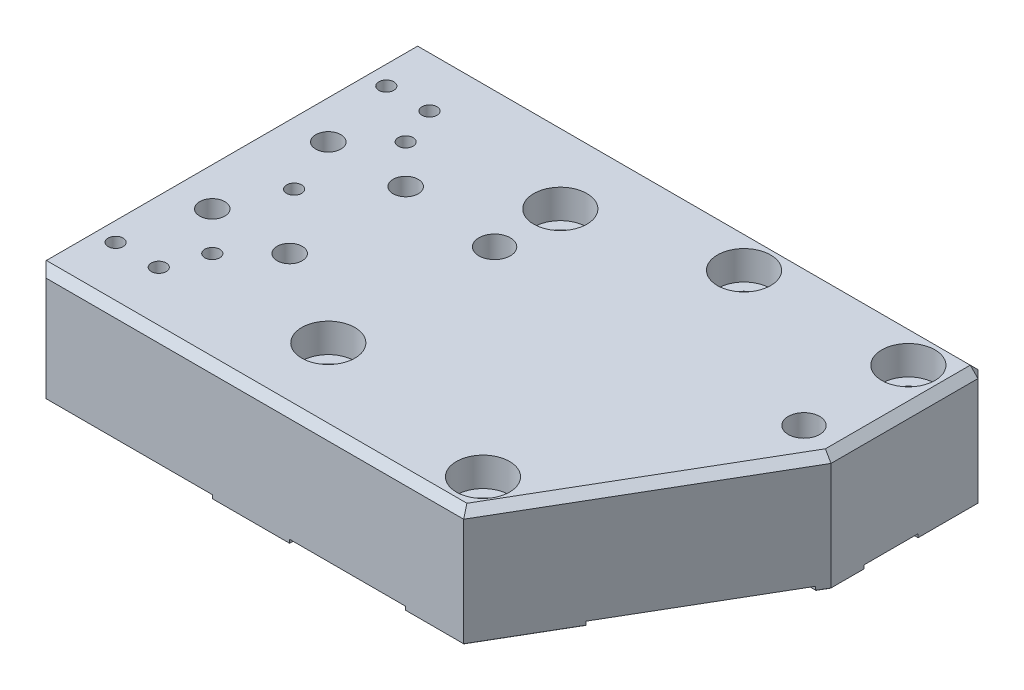
SolidWorks part; units mm, degrees
material "6061-T6 Al"
ref_plane "Front" through (0, 0, 0) normal (0, 0, 1) x (1, 0, 0)
ref_plane "Top" through (0, 0, 0) normal (0, 1, 0) x (1, 0, 0)
ref_plane "Right" through (0, 0, 0) normal (1, 0, 0) x (0, 0, -1)
sketch "Sketch1" plane through (0, 0, 0) normal (0, 1, 0) x (1, 0, 0)
  line L0 (69.85, -63.5) -> (114.3, 12.7)
  line L1 (-69.85, 63.5) -> (114.3, 63.5)
  line L2 (-69.85, 63.5) -> (-69.85, -63.5)
  line L3 (-69.85, -63.5) -> (69.85, -63.5)
  line L4 (114.3, 12.7) -> (114.3, 63.5)
  point P0 (0, 0)
  dimension "D1" = 127
  dimension "D2" = 139.7
  dimension "D3" = 69.85
  dimension "D4" = 63.5
  dimension "D5" = 184.15
  dimension "D6" = 50.8
extrude "Extrude1" add sketch "Sketch1" along normal blind 38.1
sketch "Sketch2" plane through (0, 0, 0) normal (0, -1, 0) x (1, 0, 0)
  line L0 (-44.45, -30.1625) -> (-44.45, -33.3375) construction
  line L1 (-42.8549, -30.1625) -> (-42.8549, -33.3375)
  line L2 (-46.0451, -30.1625) -> (-46.0451, -33.3375)
  circle A0 centre (-44.45, 31.75) radius 1.5951
  arc A1 (-42.8549, -30.1625) -> (-46.0451, -30.1625) centre (-44.45, -30.1625) ccw
  arc A2 (-46.0451, -33.3375) -> (-42.8549, -33.3375) centre (-44.45, -33.3375) ccw
  point P7 (-44.45, -31.75)
  dimension "D1" = 3.1902
  dimension "D3" = 31.75
  dimension "D4" = 44.45
  dimension "D6" = 31.75
  dimension "D7" = 3.175
extrude "Pin & Slot holes to Magnet block" cut sketch "Sketch2" against normal blind 6.35
sketch "Sketch3" plane through (0, 0, 0) normal (0, -1, 0) x (1, 0, 0)
  line L4 (-69.85, -63.5) -> (-69.85, 63.5) construction
  line L6 (114.3, -63.5) -> (-69.85, -63.5) construction
  line L7 (-69.85, 63.5) -> (69.85, 63.5) construction
  line L8 (114.3, -23.495) -> (114.3, -41.275)
  line L10 (114.3, -12.7) -> (114.3, -63.5) construction
  line L12 (-69.85, -63.5) -> (-69.85, -23.8125)
  line L13 (112.4479, -9.525) -> (84.6667, 38.1)
  line L14 (91.44, -63.5) -> (57.15, -63.5)
  line L15 (-69.85, 63.5) -> (-12.7, 63.5)
  line L16 (-12.7, 63.5) -> (-12.7, -63.5)
  line L17 (69.85, 63.5) -> (114.3, -12.7) construction
  line L18 (38.1, -63.5) -> (38.1, -41.275)
  line L19 (91.44, -9.525) -> (112.4479, -9.525)
  line L20 (91.44, -9.525) -> (91.44, -23.495)
  line L21 (0, 0) -> (57.15, 0) construction
  line L22 (91.44, -23.495) -> (114.3, -23.495)
  line L24 (38.1, -41.275) -> (57.15, -41.275)
  line L25 (12.7, -63.5) -> (12.7, 63.5)
  line L26 (12.7, 63.5) -> (50.8, 63.5)
  line L27 (57.15, -41.275) -> (57.15, -63.5)
  line L28 (-12.7, -63.5) -> (-69.85, -63.5)
  line L29 (-69.85, 23.8125) -> (-69.85, 63.5)
  line L30 (-69.85, -23.8125) -> (-50.8, -23.8125)
  line L31 (-50.8, -23.8125) -> (-50.8, -14.2875)
  line L32 (-69.85, -14.2875) -> (-50.8, -14.2875)
  line L33 (-19.05, -23.8125) -> (-19.05, -14.2875)
  line L34 (-19.05, -23.8125) -> (-38.1, -23.8125)
  line L35 (-38.1, -23.8125) -> (-38.1, -14.2875)
  line L36 (-19.05, -14.2875) -> (-38.1, -14.2875)
  line L37 (38.1, -63.5) -> (12.7, -63.5)
  line L39 (-69.85, 14.2875) -> (-50.8, 14.2875)
  line L40 (-50.8, 14.2875) -> (-50.8, 23.8125)
  line L41 (-69.85, 23.8125) -> (-50.8, 23.8125)
  line L42 (-19.05, 14.2875) -> (-19.05, 23.8125)
  line L43 (-19.05, 14.2875) -> (-38.1, 14.2875)
  line L44 (-38.1, 14.2875) -> (-38.1, 23.8125)
  line L45 (-19.05, 23.8125) -> (-38.1, 23.8125)
  line L46 (-48.26, -37.465) -> (-48.26, -26.035)
  line L47 (-48.26, -37.465) -> (-40.64, -37.465)
  line L48 (-40.64, -37.465) -> (-40.64, -26.035)
  line L49 (-48.26, -26.035) -> (-40.64, -26.035)
  line L50 (-48.26, 27.94) -> (-48.26, 35.56)
  line L51 (-48.26, 27.94) -> (-40.64, 27.94)
  line L52 (-40.64, 27.94) -> (-40.64, 35.56)
  line L53 (-48.26, 35.56) -> (-40.64, 35.56)
  line L54 (84.6667, 38.1) -> (50.8, 38.1)
  line L55 (50.8, 38.1) -> (50.8, 63.5)
  line L58 (114.3, -41.275) -> (91.44, -41.275)
  line L59 (91.44, -41.275) -> (91.44, -63.5)
  line L63 (-69.85, -14.2875) -> (-69.85, 14.2875)
  circle A0 centre (-44.45, 31.75) radius 1.5951 construction
  dimension "D24" = 3.81
  dimension "D2" = 25.4
  dimension "D3" = 50.8
  dimension "D4" = 91.44
  dimension "D6" = 9.525
  dimension "D7" = 9.525
  dimension "D8" = 50.8
  dimension "D9" = 7.62
  dimension "D10" = 14.2875
  dimension "D11" = 14.2875
  dimension "D12" = 50.8
  dimension "D13" = 40.64
  dimension "D14" = 27.94
  dimension "D15" = 11.43
  dimension "D16" = 26.035
  dimension "D17" = 41.275
  dimension "D18" = 38.1
  dimension "D19" = 13.97
  dimension "D21" = 19.05
  dimension "D22" = 38.1
  dimension "D23" = 12.7
extrude "Extrude3" cut sketch "Sketch3" against normal blind 1.27
hole_wizard "Tapped Hole for 1/4-20 Helicoil1" positions "Sketch9" profile "Sketch8" tap size "1/4-20" standard "Helicoil® Inch"
sketch "Sketch9" plane through (-69.85, 0, 0) normal (-1, 0, 0) x (0, 0, 1)
  point P0 (0, 30.48)
  point P3 (44.45, 8.255)
  point P6 (-44.45, 8.255)
  dimension "D1" = 8.255
  dimension "D2" = 30.48
  dimension "D3" = 44.45
  dimension "D4" = 88.9
sketch "Sketch8" plane through (-69.85, 30.48, 0) normal (0, 1, 0) x (0, 0, 1)
  line L0 (0, 0) -> (0, 22.553)
  line L1 (0, 22.553) -> (3.3782, 20.5232)
  line L2 (3.3782, 20.5232) -> (3.3782, 11.6586)
  line L3 (3.3782, 11.6586) -> (4.0475, 11.6586)
  line L5 (4.0475, 11.6586) -> (4.0475, 0.3975)
  line L6 (4.0475, 0.3975) -> (4.445, 0)
  line L7 (4.445, 0) -> (0, 0)
  line L8 (-4.0475, 0.3975) -> (-4.445, 0) construction
  line L10 (0, 22.553) -> (-3.3782, 20.5232) construction
  line L11 (0, -6.35) -> (0, 107.95) construction
  dimension "Tap Drill Dia." = 6.7564
  dimension "Tap Drill Depth" = 20.5232
  dimension "Thread Major Dia." = 8.095
  dimension "Thread Depth" = 11.6586
  dimension "Near C'Sink Dia." = 8.89
  dimension "Near C'Sink Angle" = 90
  dimension "Drill Angle" = 118
sketch "Sketch13" plane through (0, 0, 0) normal (0, -1, 0) x (1, 0, 0)
  line L0 (98.425, -16.51) -> (104.775, -16.51) construction
  line L1 (98.425, -13.3261) -> (104.775, -13.3261)
  line L2 (98.425, -19.6939) -> (104.775, -19.6939)
  circle A0 centre (0, -16.51) radius 3.1839
  arc A1 (98.425, -13.3261) -> (98.425, -19.6939) centre (98.425, -16.51) ccw
  arc A2 (104.775, -19.6939) -> (104.775, -13.3261) centre (104.775, -16.51) ccw
  circle A3 centre (101.6, -16.51) radius 3.1839 construction
  point P4 (101.6, -16.51)
  dimension "D1" = 6.3678
  dimension "D3" = 16.51
  dimension "D4" = 6.35
  dimension "D5" = 101.6
extrude "Pin & Slot holes to Stage2" cut sketch "Sketch13" against normal blind 12.7
hole_wizard "3/8 Clearance Hole1" positions "Sketch15" profile "Sketch14" hole size "3/8" standard "Ansi Inch"
sketch "Sketch15" plane through (0, 38.1, 0) normal (0, 1, 0) x (-1, 0, 0)
  line L0 (-101.6, -19.6939) -> (-101.6, -13.3261) construction
  line L1 (-98.425, -19.6939) -> (-104.775, -19.6939) construction
  line L2 (-104.775, -13.3261) -> (-98.425, -13.3261) construction
  point P0 (0, -16.51)
  point P3 (-101.6, -16.51)
sketch "Sketch14" plane through (0, 38.1, -16.51) normal (1, 0, 0) x (0, 0, 1)
  line L0 (0, 0) -> (0, 28.4997)
  line L1 (0, 28.4997) -> (5.1587, 25.4)
  line L2 (5.1587, 25.4) -> (5.1587, 0)
  line L5 (5.1587, 0) -> (0, 0)
  line L10 (0, 28.4997) -> (-5.1587, 25.4) construction
  line L11 (0, -6.35) -> (0, 107.95) construction
  dimension "Hole Dia." = 10.3175
  dimension "Hole Depth" = 25.4
  dimension "Drill Angle" = 118
sketch "Sketch16" plane through (-69.85, 0, 0) normal (-1, 0, 0) x (0, 0, 1)
  line L0 (-42.8625, 16.51) -> (-46.0375, 16.51) construction
  line L1 (-42.8625, 14.9149) -> (-46.0375, 14.9149)
  line L2 (-42.8625, 18.1051) -> (-46.0375, 18.1051)
  line L3 (44.45, 8.255) -> (44.45, 16.51) construction
  line L4 (-44.45, 8.255) -> (-44.45, 16.51) construction
  circle A0 centre (44.45, 16.51) radius 1.5951
  arc A1 (-42.8625, 14.9149) -> (-42.8625, 18.1051) centre (-42.8625, 16.51) ccw
  arc A2 (-46.0375, 18.1051) -> (-46.0375, 14.9149) centre (-46.0375, 16.51) ccw
  circle A4 centre (44.45, 8.255) radius 4.0475 construction
  point P5 (-44.45, 16.51)
  dimension "D3" = 3.1902
  dimension "D4" = 8.255
  dimension "D2" = 3.175
extrude "Pin & Slot holes, tooling btacket" cut sketch "Sketch16" against normal blind 6.35
hole_wizard "#8 Clearance Hole1" positions "Sketch12" profile "Sketch11" hole size "#8" standard "Ansi Inch"
sketch "Sketch12" plane through (0, 38.1, 0) normal (0, 1, 0) x (-1, 0, 0)
  line L2 (49.3268, 47.8282) -> (49.3268, 41.0718) construction
  line L3 (49.3268, -41.0718) -> (49.3268, -47.8282) construction
  point P0 (44.45, 31.75)
  point P3 (44.45, -31.75)
  point P12 (49.3268, 44.45)
  point P16 (49.3268, -44.45)
  dimension "D1" = 31.75
sketch "Sketch11" plane through (-44.45, 38.1, 31.75) normal (1, 0, 0) x (0, 0, 1)
  line L0 (0, 0) -> (0, 33.2266)
  line L1 (0, 33.2266) -> (2.4574, 31.75)
  line L2 (2.4574, 31.75) -> (2.4574, 0)
  line L5 (2.4574, 0) -> (0, 0)
  line L10 (0, 33.2266) -> (-2.4575, 31.75) construction
  line L11 (0, -6.35) -> (0, 107.95) construction
  dimension "Hole Dia." = 4.9149
  dimension "Hole Depth" = 31.75
  dimension "Drill Angle" = 118
hole_wizard "#8 Clearance Hole2" positions "Sketch18" profile "Sketch17" hole size "#8" standard "Ansi Inch"
sketch "Sketch18" plane through (0, 38.1, 0) normal (0, 1, 0) x (-1, 0, 0)
  line L0 (63.5, -42.8625) -> (63.5, -46.0375) construction
  line L1 (63.5, 42.8549) -> (63.5, 46.0451) construction
  point P0 (63.5, -44.45)
  point P4 (63.5, 44.45)
sketch "Sketch17" plane through (-63.5, 38.1, -44.45) normal (1, 0, 0) x (0, 0, 1)
  line L0 (0, 0) -> (0, 24.3366)
  line L1 (0, 24.3366) -> (2.4574, 22.86)
  line L2 (2.4574, 22.86) -> (2.4574, 0)
  line L5 (2.4574, 0) -> (0, 0)
  line L10 (0, 24.3366) -> (-2.4575, 22.86) construction
  line L11 (0, -6.35) -> (0, 107.95) construction
  dimension "Hole Dia." = 4.9149
  dimension "Hole Depth" = 22.86
  dimension "Drill Angle" = 118
hole_wizard "#8 Clearance Hole3" positions "Sketch20" profile "Sketch19" hole size "#8" standard "Ansi Inch"
sketch "Sketch20" plane through (0, 38.1, 0) normal (0, 1, 0) x (-1, 0, 0)
  line L0 (49.3268, 3.3782) -> (49.3268, -3.3782) construction
  point P0 (49.3268, 0)
sketch "Sketch19" plane through (-49.3268, 38.1, 0) normal (1, 0, 0) x (0, 0, 1)
  line L0 (0, 0) -> (0, 11.6366)
  line L1 (0, 11.6366) -> (2.4574, 10.16)
  line L2 (2.4574, 10.16) -> (2.4574, 0)
  line L5 (2.4574, 0) -> (0, 0)
  line L10 (0, 11.6366) -> (-2.4575, 10.16) construction
  line L11 (0, -6.35) -> (0, 107.95) construction
  dimension "Hole Dia." = 4.9149
  dimension "Hole Depth" = 10.16
  dimension "Drill Angle" = 118
hole_wizard "CBORE for 3/8 Socket Head Cap Screw1" positions "Sketch7" profile "Sketch6" counterbore size "3/8" standard "Ansi Inch"
sketch "Sketch7" plane through (0, 38.1, 0) normal (0, 1, 0) x (-1, 0, 0)
  point P0 (0, 38.1)
  point P25 (0, -38.1)
  point P27 (-63.5, 50.8)
  point P30 (-101.6, -50.8)
  point P44 (-47.625, -50.8)
  dimension "D1" = 63.5
  dimension "D2" = 101.6
  dimension "D3" = 38.1
  dimension "D4" = 38.1
  dimension "D5" = 50.8
  dimension "D7" = 50.8
  dimension "D8" = 47.625
sketch "Sketch6" plane through (0, 38.1, 38.1) normal (1, 0, 0) x (0, 0, 1)
  line L0 (0, 0) -> (0, 38.1)
  line L1 (0, 38.1) -> (5.0419, 38.1)
  line L3 (5.0419, 38.1) -> (5.0419, 9.525)
  line L4 (5.0419, 9.525) -> (8.7312, 9.525)
  line L5 (8.7312, 9.525) -> (8.7312, 0)
  line L7 (8.7312, 0) -> (0, 0)
  line L11 (0, -6.35) -> (0, 107.95) construction
  dimension "Thru Hole Dia." = 10.0838
  dimension "Thru Hole Depth" = 38.1
  dimension "C'Bore Dia." = 17.4625
  dimension "C'Bore Depth" = 9.525
hole_wizard "CBORE for #8 Socket Head Cap Screw1" positions "Sketch5" profile "Sketch4" counterbore size "#8" standard "Ansi Inch"
sketch "Sketch5" plane through (0, 38.1, 0) normal (0, 1, 0) x (-1, 0, 0)
  line L0 (44.45, 31.75) -> (44.45, -33.3375) construction
  line L2 (53.34, 0) -> (0, 0) construction
  point P0 (57.15, 19.05)
  point P2 (31.75, 19.05)
  point P4 (31.75, -19.05)
  point P6 (57.15, -19.05)
  dimension "D1" = 25.4
  dimension "D2" = 38.1
  dimension "D3" = 12.7
  dimension "D4" = 19.05
sketch "Sketch4" plane through (-57.15, 38.1, 19.05) normal (1, 0, 0) x (0, 0, 1)
  line L0 (0, 0) -> (0, 38.1)
  line L1 (0, 38.1) -> (2.4574, 38.1)
  line L3 (2.4574, 38.1) -> (2.4575, 5.842)
  line L4 (2.4575, 5.842) -> (4.1275, 5.842)
  line L5 (4.1275, 5.842) -> (4.1275, 0)
  line L7 (4.1275, 0) -> (0, 0)
  line L11 (0, -6.35) -> (0, 107.95) construction
  dimension "Thru Hole Dia." = 4.9149
  dimension "Thru Hole Depth" = 38.1
  dimension "C'Bore Dia." = 8.255
  dimension "C'Bore Depth" = 5.842
chamfer "Chamfer2" distance 2.286 angle 45 5 edges at (101.6, 0, -19.6939) (107.9589, 0, -16.51) (95.2411, 0, -16.51) (101.6, 0, -13.3261) (0, 0, -19.6939)
chamfer "Chamfer1" distance 2.54 angle 45 9 edges at (-69.85, 38.1, 0) (22.225, 38.1, -63.5) (0, 38.1, 63.5) (-69.85, 19.685, -63.5) (114.3, 19.05, -63.5) (69.85, 19.05, 63.5) (-69.85, 19.685, 63.5) (114.3, 38.1, -38.1) (92.075, 38.1, 25.4)
chamfer "Chamfer3" distance 0.127 angle 45 56 edges at (38.1, 0, -52.3875) (47.625, 0, -41.275) (57.15, 0, -52.3875) (47.625, 0, -63.5) (47.625, 0, -45.7581) (91.44, 0, -52.3875) (102.87, 0, -41.275) (114.3, 0, -51.1175) (113.03, 0, -62.23) (101.6, 0, -63.5) (101.6, 0, -45.7581) (77.2583, 0, 50.8) (67.7333, 0, 38.1) (50.8, 0, 50.8) (60.325, 0, 63.5) (63.5, 0, 55.8419) (-48.26, 0, 31.75) (-44.45, 0, 35.56) (-40.64, 0, 31.75) (-44.45, 0, 27.94) (-48.26, 0, -31.75) (-44.45, 0, -26.035) (-40.64, 0, -31.75) (-44.45, 0, -37.465) (-60.325, 0, -14.2875) (-50.8, 0, -19.05) (-60.325, 0, -23.8125) (-69.85, 0, -19.05) (-57.15, 0, -16.5926) (-38.1, 0, -19.05) (-28.575, 0, -14.2875) (-19.05, 0, -19.05) (-28.575, 0, -23.8125) (-31.75, 0, -16.5926) (-38.1, 0, 19.05) (-28.575, 0, 23.8125) (-19.05, 0, 19.05) (-28.575, 0, 14.2875) (-31.75, 0, 21.5074) (102.87, 0, -23.495) (91.44, 0, -16.51) (101.944, 0, -9.525) (0, 0, 63.5) (-12.7, 0, 0) (0, 0, -63.5) (12.7, 0, 0) (0, 0, 43.1419) (0, 0, -33.0581) (-57.15, 0, 21.5074) (-50.8, 0, 19.05) (-60.325, 0, 14.2875) (-69.85, 0, 19.05) (-60.325, 0, 23.8125) (-69.85, 38.1, 0) (114.3, 0, -18.0975) (113.374, 0, -11.1125)
chamfer "Chamfer4" distance 0.762 angle 45 10 edges at (-44.45, 0, 30.1549) (-44.45, 0, -34.9326) (-42.8549, 0, -31.75) (-46.0451, 0, -31.75) (-44.45, 0, -28.5674) (-69.85, 16.51, 46.0451) (-69.85, 16.51, -47.6326) (-69.85, 14.9149, -44.45) (-69.85, 18.1051, -44.45) (-69.85, 16.51, -41.2674)
